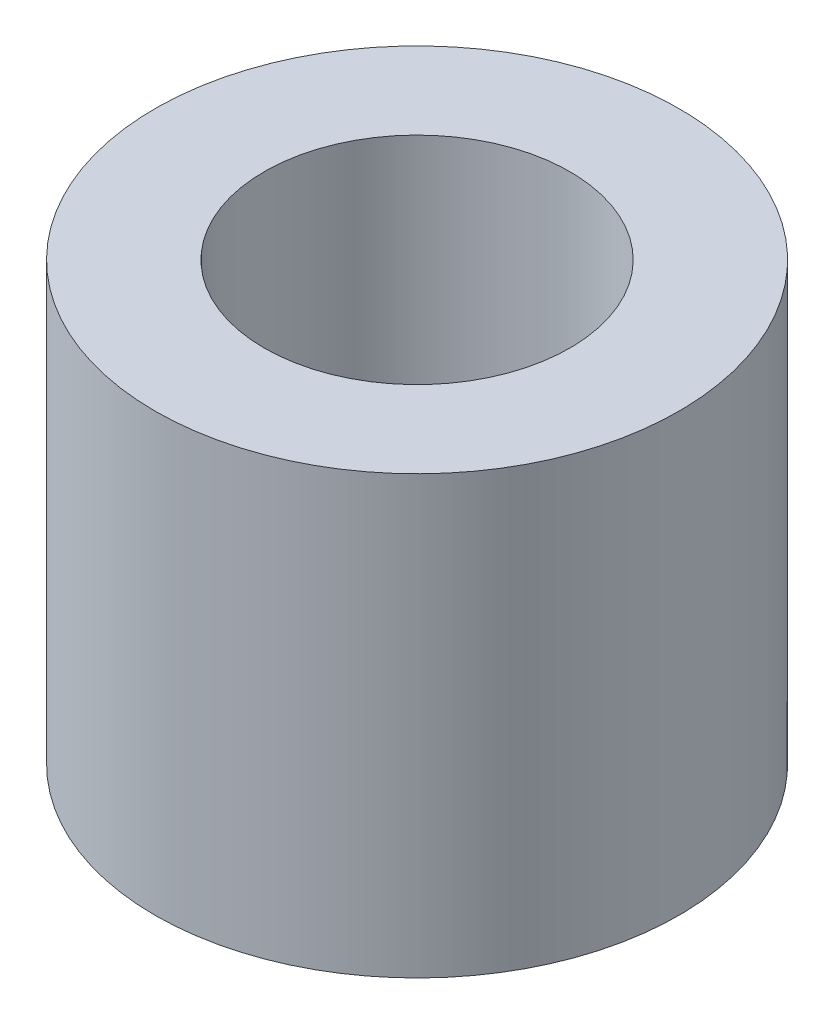
SolidWorks part; units mm, degrees
ref_plane "Front Plane" through (0, 0, 0) normal (0, 0, 1) x (1, 0, 0)
ref_plane "Top Plane" through (0, 0, 0) normal (0, 1, 0) x (1, 0, 0)
ref_plane "Right Plane" through (0, 0, 0) normal (1, 0, 0) x (0, 0, -1)
sketch "Sketch1" plane through (0, 0, 0) normal (0, 1, 0) x (1, 0, 0)
  circle A0 centre (0, 0) radius 3
  circle A1 centre (0, 0) radius 1.75
  dimension "D1" = 6
  dimension "D2" = 3.5
extrude "Boss-Extrude1" add sketch "Sketch1" along normal blind 5
